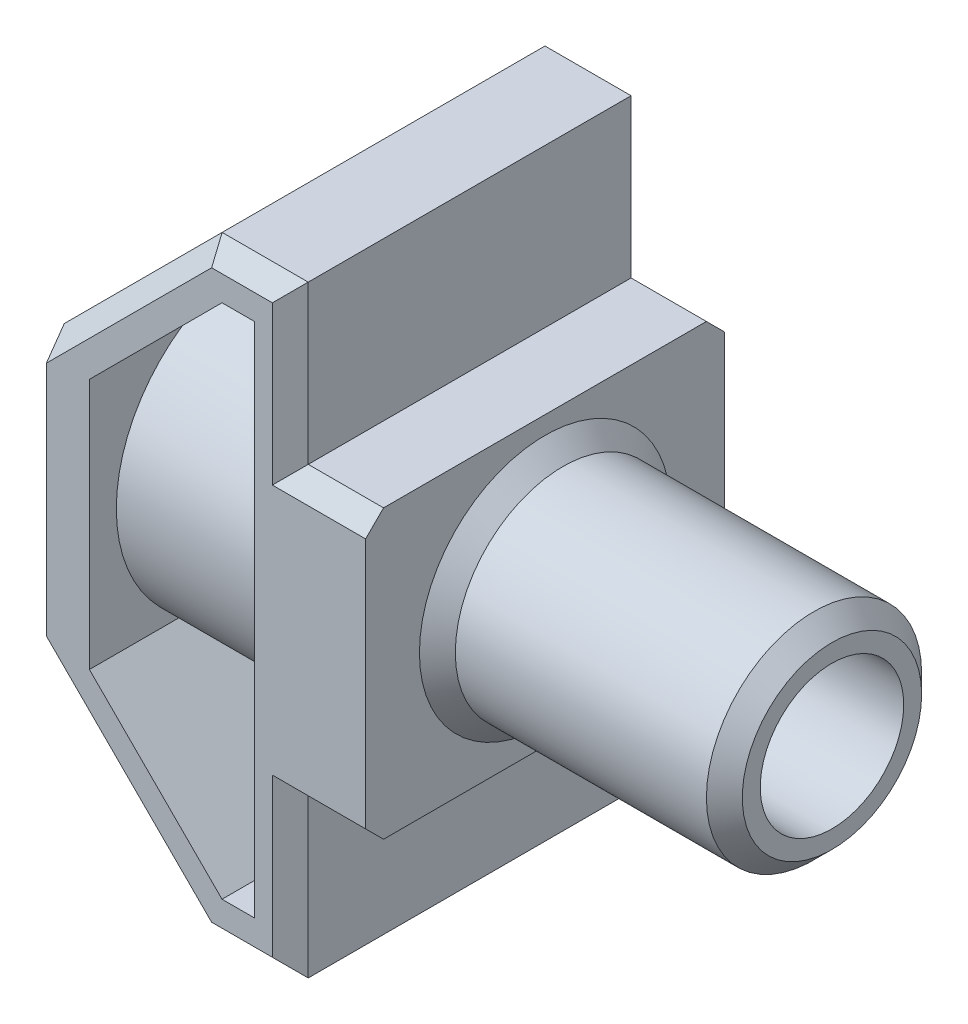
SolidWorks part; units mm, degrees
ref_plane "Alzado" through (0, 0, 0) normal (0, 0, 1) x (1, 0, 0)
ref_plane "Planta" through (0, 0, 0) normal (0, 1, 0) x (1, 0, 0)
ref_plane "Vista lateral" through (0, 0, 0) normal (1, 0, 0) x (0, 0, -1)
sketch "Croquis1" plane through (0, 0, 0) normal (0, 0, 1) x (1, 0, 0)
  line L0 (0, 0) -> (0, 5301.9663) construction
  line L1 (0, 0) -> (5301.9663, 0) construction
  line L2 (-4.8553, 4) -> (5297.111, 4) construction
  line L3 (0, 4) -> (-2.1, 4)
  line L4 (-8.9, 5.9678) -> (-8.9, -5295.9985) construction
  line L5 (-2.1, 7.8714) -> (-2.1, -5294.095) construction
  line L6 (-2.1, 4) -> (-2.1, 8.4)
  line L8 (-8.9, 4) -> (-8.9, -4)
  line L10 (-2.1, -4) -> (-2.1, -8.4)
  line L11 (0, -4) -> (-2.1, -4)
  line L12 (0, 4) -> (0, -4)
  line L13 (-4.5, -15.5102) -> (-4.5, 49984.4898) construction
  line L14 (-2.1, -8.4) -> (-4.5, -8.4)
  line L15 (-4.5, -8.4) -> (-8.9, -4)
  line L16 (-4.5, 8.4) -> (-8.9, 4)
  line L17 (-2.1, 8.4) -> (-4.5, 8.4)
  point P17 (-8.9, 0)
  dimension "D1" = 8
  dimension "D2" = 6.8
  dimension "D3" = 2.1
  dimension "D4" = 8
  dimension "D5" = 16.8
  dimension "D6" = 2.4
extrude "Saliente-Extruir1" add sketch "Croquis1" along normal mid plane 10
sketch "Croquis2" plane through (0, 0, 0) normal (1, 0, 0) x (0, 0, -1)
  circle A0 centre (0, 0) radius 3
  dimension "D1" = 6
extrude "Saliente-Extruir2" add sketch "Croquis2" along normal blind 8
chamfer "Chaflán1" distance 0.5 angle 45 2 edges at (8, 0, -3) (0, 0, -3)
sketch "Croquis3" plane through (8, 0, 0) normal (1, 0, 0) x (0, 0, -1)
  circle A0 centre (0, 0) radius 2
  dimension "D1" = 4
extrude "Cortar-Extruir1" cut sketch "Croquis3" against normal through all
sketch "Croquis4" plane through (-8.9, 0, 0) normal (-1, 0, 0) x (0, 0, 1)
  circle A0 centre (0, 0) radius 3.45
  dimension "D1" = 6.9
extrude "Cortar-Extruir2" cut sketch "Croquis4" against normal blind 6.5
sketch "Croquis5" plane through (0, 0, 5) normal (0, 0, 1) x (1, 0, 0)
  line L0 (-3.1, 7.2) -> (-3.1, -7.2)
  line L3 (-7.7, -3.5029) -> (-7.7, 3.5029)
  line L4 (-7.7, 3.5029) -> (-4.0029, 7.2)
  line L5 (-4.0029, 7.2) -> (-3.1, 7.2)
  line L6 (0, 0) -> (-50000, 0) construction
  line L7 (0, -4) -> (0, 4) construction
  line L8 (-4.0029, -7.2) -> (-3.1, -7.2)
  line L9 (-7.7, -3.5029) -> (-4.0029, -7.2)
  line L10 (-2.1, 4) -> (-2.1, 8.4) construction
  line L11 (-2.1, 8.4) -> (-4.5, 8.4) construction
  line L12 (-4.5, 8.4) -> (-8.9, 4) construction
  line L13 (-8.9, 4) -> (-8.9, -4) construction
  point P9 (0, 0)
  point P13 (-7.497, -4.0793)
  point P14 (-2.9365, -6.9668)
  point P22 (-7.6221, -3.5905)
  point P23 (-7.7, -2.6813)
  point P24 (-7.7, -3.3459)
  dimension "D1" = 1
  dimension "D2" = 1.2
  dimension "D3" = 1.2
  dimension "D4" = 1.2
extrude "Cortar-Extruir3" cut sketch "Croquis5" against normal through all
chamfer "Chaflán2" distance 0.5 angle 45 16 edges at (-6.7, -6.2, 5) (-3.3, -8.4, 5) (-2.1, -6.2, 5) (-1.05, -4, 5) (-1.05, 4, 5) (-2.1, 6.2, 5) (-6.7, 6.2, 5) (-3.3, 8.4, 5) (-1.05, 4, -5) (-6.7, 6.2, -5) (-3.3, 8.4, -5) (-2.1, 6.2, -5) (-1.05, -4, -5) (-2.1, -6.2, -5) (-6.7, -6.2, -5) (-3.3, -8.4, -5)
chamfer "Chaflán3" distance 1.2 angle 45 1 edges at (-2.4, 0, 2)
sketch "Croquis6" plane through (-8.9, 0, 0) normal (-1, 0, 0) x (0, 0, 1)
  circle A0 centre (0, 0) radius 3.45
  circle A1 centre (0, 0) radius 4.25
  dimension "D1" = 0.8
extrude "Saliente-Extruir3" add sketch "Croquis6" against normal up to surface (4.8 mm away) from offset 1 up to face at (-3.1, 0, 0) offset against normal yes
